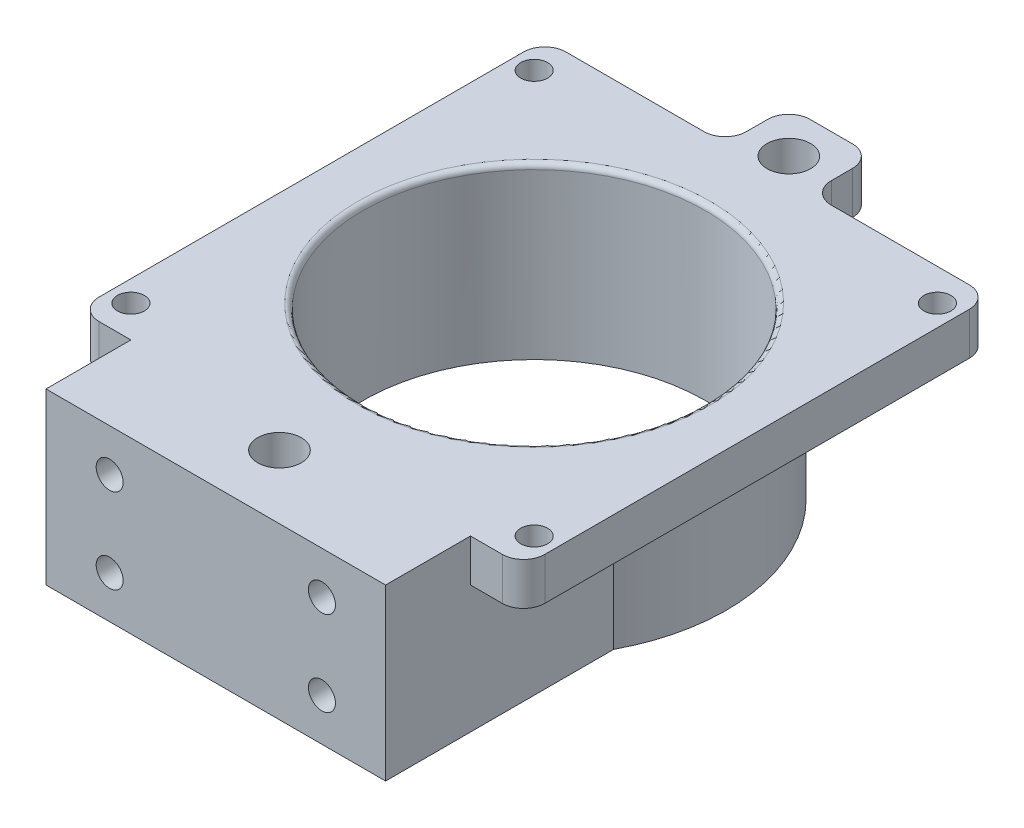
SolidWorks part; units mm, degrees
ref_plane "Front Plane" through (0, 0, 0) normal (0, 0, 1) x (1, 0, 0)
ref_plane "Top Plane" through (0, 0, 0) normal (0, 1, 0) x (1, 0, 0)
ref_plane "Right Plane" through (0, 0, 0) normal (1, 0, 0) x (0, 0, -1)
sketch "Sketch1" plane through (0, 0, 0) normal (0, 1, 0) x (1, 0, 0)
  line L0 (0, 25.5905) -> (0, 28.7655) construction
  circle A1 centre (0, 0) radius 28.7655
  dimension "D1" = 57.531
extrude "Boss-Extrude1" add sketch "Sketch1" along normal blind 19.05
ref_plane "Plane2" through (0, 19.05, 0) normal (0, 1, 0) x (1, 0, 0)
sketch "Sketch4" plane through (0, 19.05, 0) normal (0, 1, 0) x (1, 0, 0)
  line L0 (0, -54.6174) -> (0, -41.9174) construction
  line L1 (-33.3375, 34.925) -> (-6.35, 34.925)
  line L2 (-33.3375, 34.925) -> (-33.3375, -34.925)
  line L3 (-33.3375, -34.925) -> (33.3375, -34.925)
  line L4 (33.3375, 34.925) -> (33.3375, -34.925)
  line L5 (-33.3375, 34.925) -> (33.3375, -34.925) construction
  line L6 (-33.3375, -34.925) -> (33.3375, 34.925) construction
  line L7 (-6.35, 44.45) -> (6.35, 44.45)
  line L8 (-6.35, 44.45) -> (-6.35, 34.925)
  line L10 (6.35, 44.45) -> (6.35, 34.925)
  line L11 (-6.35, 44.45) -> (6.35, 34.925) construction
  line L12 (-6.35, 34.925) -> (6.35, 44.45) construction
  line L13 (6.35, 34.925) -> (33.3375, 34.925)
  point P0 (0, 0)
  point P6 (0, 39.6875)
  dimension "D1" = 69.85
  dimension "D2" = 12.7
  dimension "D3" = 9.525
extrude "Boss-Extrude2" add sketch "Sketch4" along normal blind 6.35 separate body
fillet "Fillet1" radius 3.175 8 edges at (33.3375, 22.225, -34.925) (6.35, 22.225, -34.925) (6.35, 22.225, -44.45) (-6.35, 22.225, -34.925) (-6.35, 22.225, -44.45) (-33.3375, 22.225, -34.925) (-33.3375, 22.225, 34.925) (33.3375, 22.225, 34.925)
ref_plane "Plane3" through (0, 0, 47.625) normal (0, 0, 1) x (1, 0, 0)
sketch "Sketch8" plane through (0, 0, 47.625) normal (0, 0, 1) x (1, 0, 0)
  line L0 (0, -4.5989) -> (0, 29.9989) construction
  line L1 (25.4, 0) -> (-25.4, 0)
  line L2 (25.4, 0) -> (25.4, 25.4)
  line L3 (25.4, 25.4) -> (-25.4, 25.4)
  line L4 (-25.4, 0) -> (-25.4, 25.4)
  line L5 (-25.4, 12.7) -> (0, 12.7) construction
  line L6 (0, 12.7) -> (25.4, 12.7) construction
  dimension "D1" = 25.4
  dimension "D2" = 50.8
extrude "Boss-Extrude4" add sketch "Sketch8" against normal blind 38.1
sketch "Sketch5" plane through (0, 25.4, 0) normal (0, 1, 0) x (1, 0, 0)
  circle A0 centre (0, 0) radius 25.5905
  dimension "D1" = 51.181
extrude "Cut-Extrude1" cut sketch "Sketch5" against normal through all contours A0
fillet "Fillet2" radius 0.7937 1 edges at (0, 25.4, 25.5905)
hole_wizard "#10-32 Tapped Hole1" positions "Sketch10" profile "Sketch9" tap size "#10-32" standard "ANSI Inch" end condition up to next
sketch "Sketch10" plane through (0, 25.4, 0) normal (0, 1, 0) x (1, 0, 0)
  line L0 (-30.1625, 30.1625) -> (30.1625, 30.1625) construction
  line L1 (30.1625, 30.1625) -> (30.1625, -30.1625) construction
  line L2 (30.1625, -30.1625) -> (-30.1625, -30.1625) construction
  line L3 (-30.1625, -30.1625) -> (-30.1625, 30.1625) construction
  line L6 (-30.1625, 30.1625) -> (0, 0) construction
  line L7 (0, 0) -> (30.1625, -30.1625) construction
  line L9 (33.3375, -31.75) -> (33.3375, 31.75) construction
  point P0 (-30.1625, 30.1625)
  point P2 (30.1625, 30.1625)
  point P4 (30.1625, -30.1625)
  point P6 (-30.1625, -30.1625)
  dimension "D1" = 3.175
sketch "Sketch9" plane through (-30.1625, 25.4, -30.1625) normal (1, 0, 0) x (0, 0, 1)
  line L0 (0, 0) -> (0, 6.35)
  line L1 (0, 6.35) -> (2.0193, 6.35)
  line L2 (2.0193, 6.35) -> (2.0193, 0)
  line L5 (2.0193, 0) -> (0, 0)
  line L11 (0, -6.35) -> (0, 107.95) construction
  dimension "Thru Tap Drill Dia." = 4.0386
  dimension "Thru Tap Drill Depth" = 6.35
cosmetic thread "Hole Thread1" parameters "D2"=4.826
cosmetic thread "Hole Thread2" parameters "D2"=4.826
cosmetic thread "Hole Thread3" parameters "D2"=4.826
cosmetic thread "Hole Thread4" parameters "D2"=4.826
hole_wizard "F (0.257) Diameter Hole1" positions "Sketch12" profile "Sketch11" hole size "F" standard "ANSI Inch"
sketch "Sketch12" plane through (0, 25.4, 0) normal (0, 1, 0) x (1, 0, 0)
  line L2 (0, 44.45) -> (0, -49.3464) construction
  line L3 (3.175, 44.45) -> (-3.175, 44.45) construction
  line L5 (36.3385, 0) -> (-37.0001, 0) construction
  point P0 (0, 38.1)
  point P2 (0, -38.1)
  dimension "D1" = 38.1
  dimension "D2" = 38.1
sketch "Sketch11" plane through (0, 25.4, -38.1) normal (1, 0, 0) x (0, 0, 1)
  line L0 (0, 0) -> (0, 6.35)
  line L1 (0, 6.35) -> (3.2639, 6.35)
  line L2 (3.2639, 6.35) -> (3.2639, 0)
  line L5 (3.2639, 0) -> (0, 0)
  line L11 (0, -6.35) -> (0, 107.95) construction
  dimension "Thru Hole Dia." = 6.5278
  dimension "Thru Hole Depth" = 6.35
hole_wizard "#10-32 Tapped Hole2" positions "Sketch14" profile "Sketch13" tap size "#10-32" standard "ANSI Inch"
sketch "Sketch14" plane through (0, 0, 47.625) normal (0, 0, 1) x (1, 0, 0)
  line L0 (-15.875, 19.05) -> (15.875, 19.05) construction
  line L1 (15.875, 19.05) -> (15.875, 6.35) construction
  line L2 (15.875, 6.35) -> (-15.875, 6.35) construction
  line L3 (-15.875, 6.35) -> (-15.875, 19.05) construction
  line L4 (-15.875, 19.05) -> (0, 12.7) construction
  line L5 (0, 12.7) -> (15.875, 6.35) construction
  line L10 (-25.4, 12.7) -> (25.4, 12.7) construction
  line L11 (-25.4, 25.4) -> (-25.4, 0) construction
  line L12 (25.4, 0) -> (25.4, 25.4) construction
  line L14 (0, 25.4) -> (0, 0) construction
  line L15 (25.4, 25.4) -> (-25.4, 25.4) construction
  line L16 (-25.4, 0) -> (25.4, 0) construction
  point P0 (-15.875, 19.05)
  point P2 (-15.875, 6.35)
  point P4 (15.875, 6.35)
  point P6 (15.875, 19.05)
  dimension "D1" = 15.875
  dimension "D2" = 6.35
sketch "Sketch13" plane through (-15.875, 19.05, 47.625) normal (1, 0, 0) x (0, -1, 0)
  line L0 (0, 0) -> (0, 17.9773)
  line L1 (0, 17.9773) -> (2.0193, 16.764)
  line L2 (2.0193, 16.764) -> (2.0193, 0)
  line L5 (2.0193, 0) -> (0, 0)
  line L10 (0, 17.9773) -> (-2.0193, 16.764) construction
  line L11 (0, -6.35) -> (0, 107.95) construction
  dimension "Tap Drill Dia." = 4.0386
  dimension "Tap Drill Depth" = 16.764
  dimension "Drill Angle" = 118
cosmetic thread "Hole Thread7" parameters "D1"=12.7, "D2"=4.826
cosmetic thread "Hole Thread8" parameters "D1"=12.7, "D2"=4.826
cosmetic thread "Hole Thread9" parameters "D1"=12.7, "D2"=4.826
cosmetic thread "Hole Thread10" parameters "D1"=12.7, "D2"=4.826
